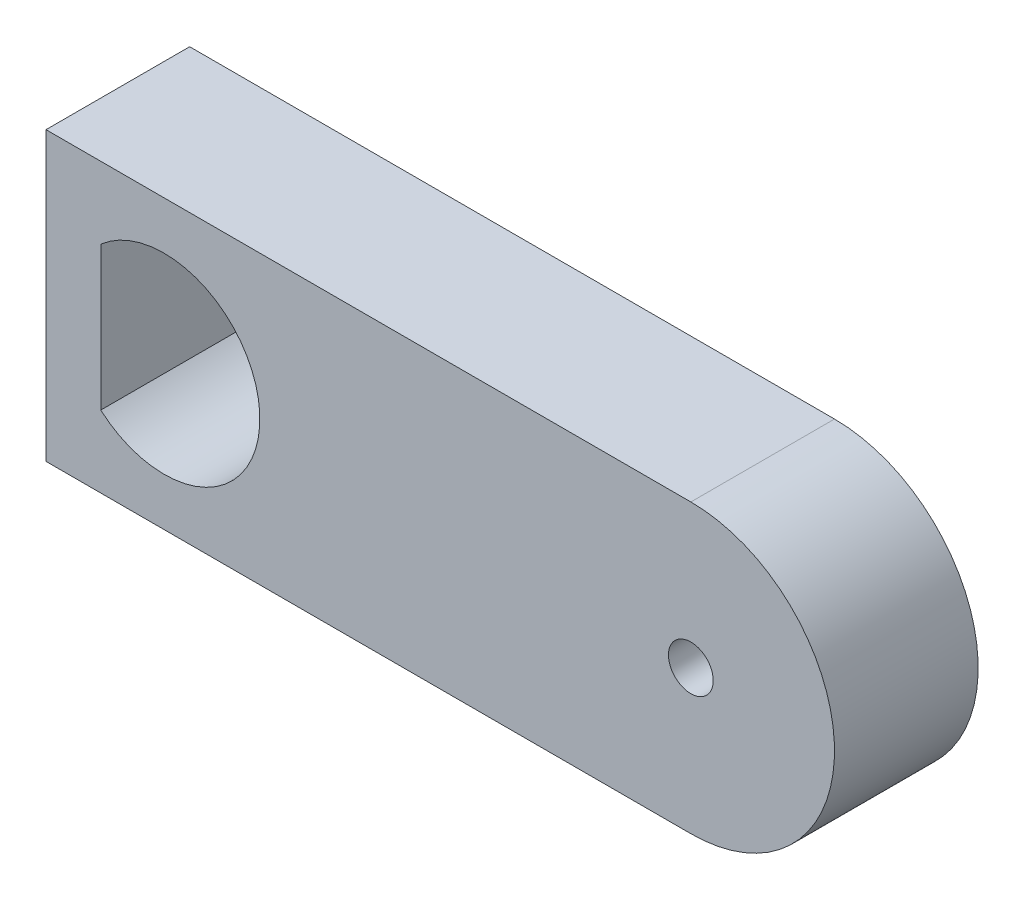
SolidWorks part; units mm, degrees
ref_plane "Front Plane" through (0, 0, 0) normal (0, 0, 1) x (1, 0, 0)
ref_plane "Top Plane" through (0, 0, 0) normal (0, 1, 0) x (1, 0, 0)
ref_plane "Right Plane" through (0, 0, 0) normal (1, 0, 0) x (0, 0, -1)
sketch "Sketch1" plane through (0, 0, 0) normal (0, 0, 1) x (1, 0, 0)
  line L0 (-6.0019, 1.5) -> (-6.0019, -1.5)
  line L1 (-7.1453, -3) -> (6.321, -3)
  line L2 (-7.1453, -3) -> (-7.1453, 3)
  line L3 (-7.1453, 3) -> (6.321, 3)
  arc A0 (6.321, -3) -> (6.321, 3) centre (6.321, 0) ccw
  arc A1 (-6.0019, -1.5) -> (-6.0019, 1.5) centre (-4.679, 0) ccw
  circle A2 centre (6.321, 0) radius 0.4677
  point P0 (0, 0)
  point P9 (0, 0)
  point P10 (-3.6724, -1.7282)
  point P12 (0, 0)
  point P13 (0, 0)
  point P15 (0, 0)
  point P16 (0, 0)
  point P17 (0, 0)
  dimension "D2" = 6
  dimension "D3" = 4
  dimension "D5" = 0
  dimension "D1" = 11
  dimension "D4" = 3
extrude "Boss-Extrude1" add sketch "Sketch1" along normal blind 3
